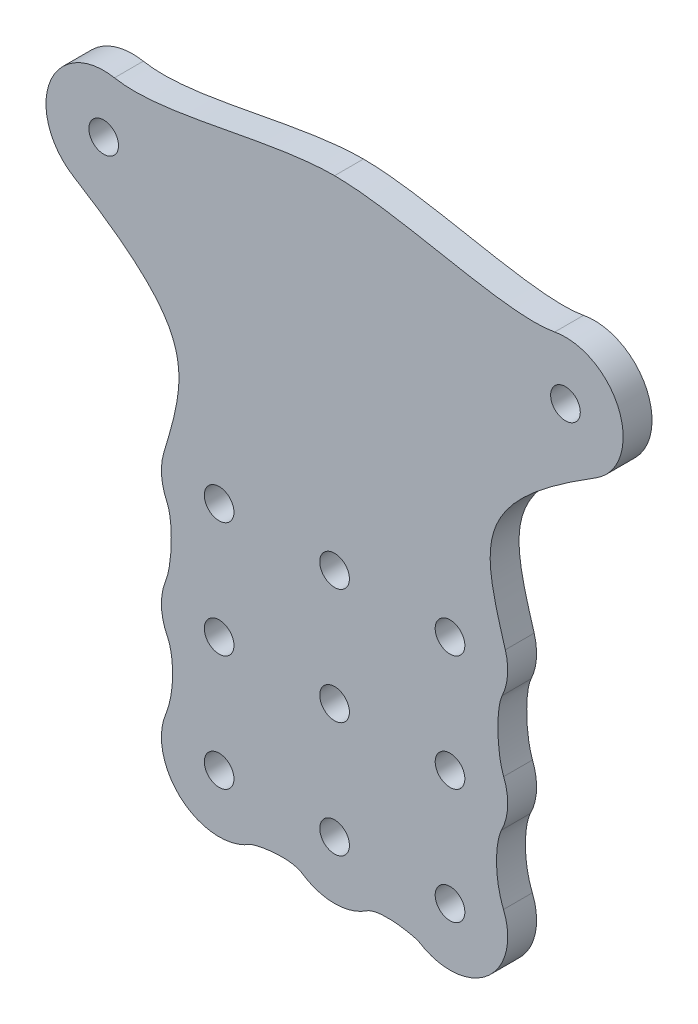
SolidWorks part; units mm, degrees
material "6061-T6 (SS)"
ref_plane "Front Plane" through (0, 0, 0) normal (0, 0, 1) x (1, 0, 0)
ref_plane "Top Plane" through (0, 0, 0) normal (0, 1, 0) x (1, 0, 0)
ref_plane "Right Plane" through (0, 0, 0) normal (1, 0, 0) x (0, 0, -1)
sketch "Sketch1" plane through (0, 0, 0) normal (0, 0, 1) x (1, 0, 0)
  line L0 (50.8, 0) -> (-50.8, 0) construction
  line L1 (0, 0) -> (0, -120.65) construction
  line L2 (63.5, 38.1) -> (-63.5, 38.1) construction
  line L3 (63.5, 38.1) -> (63.5, -38.1) construction
  line L4 (63.5, -38.1) -> (-63.5, -38.1) construction
  line L5 (-63.5, 38.1) -> (-63.5, -38.1) construction
  line L6 (63.5, 38.1) -> (-63.5, -38.1) construction
  line L7 (63.5, -38.1) -> (-63.5, 38.1) construction
  line L8 (-25.4, -57.15) -> (0, -57.15) construction
  line L9 (17.958, 18.0474) -> (-17.958, 18.0474) construction
  line L10 (-38.1, -120.65) -> (38.1, -120.65) construction
  line L11 (-38.1, -120.65) -> (-38.1, -38.1) construction
  line L12 (-38.1, -38.1) -> (38.1, -38.1) construction
  line L13 (38.1, -120.65) -> (38.1, -38.1) construction
  line L14 (-38.1, -120.65) -> (38.1, -38.1) construction
  line L15 (-38.1, -38.1) -> (38.1, -120.65) construction
  line L16 (-39.5718, 10.7947) -> (-57.2894, 14.1593) construction
  line L17 (-42.1887, -68.962) -> (-32.7709, -37.4736) construction
  line L18 (-48.3449, -16.4436) -> (-71.4207, -2.1908) construction
  line L19 (-35.193, -66.1555) -> (-38.5769, -58.9863) construction
  line L20 (-25.4, -57.15) -> (-25.4, -82.55) construction
  line L21 (-38.4283, -80.9433) -> (-35.9741, -74.7714) construction
  line L22 (-35.1425, -91.4238) -> (-38.5996, -84.5944) construction
  line L23 (-39.0166, -107.7442) -> (-35.3297, -98.6304) construction
  line L24 (-16.1907, -117.1192) -> (-21.3581, -120.4597) construction
  line L25 (-4.5266, -120.1946) -> (-9.5559, -116.8441) construction
  circle A0 centre (-50.8, 0) radius 3.2639
  circle A1 centre (50.8, 0) radius 3.2639
  circle A2 centre (-25.4, -57.15) radius 3.2639
  circle A3 centre (0, -57.15) radius 3.2639
  circle A4 centre (25.4, -57.15) radius 3.2639
  circle A5 centre (0, -82.55) radius 3.2639
  circle A6 centre (25.4, -82.55) radius 3.2639
  circle A7 centre (0, -107.95) radius 3.2639
  circle A8 centre (25.4, -107.95) radius 3.2639
  circle A9 centre (-25.4, -82.55) radius 3.2639
  circle A10 centre (-25.4, -107.95) radius 3.2639
  circle A11 centre (-50.8, 0) radius 12.7
  circle A12 centre (50.8, 0) radius 12.7
  circle A13 centre (-25.4, -57.15) radius 12.7
  circle A14 centre (0, -57.15) radius 12.7 construction
  circle A15 centre (25.4, -57.15) radius 12.7
  circle A16 centre (0, -82.55) radius 12.7 construction
  circle A17 centre (25.4, -82.55) radius 12.7
  circle A18 centre (0, -107.95) radius 12.7
  circle A19 centre (25.4, -107.95) radius 12.7
  circle A20 centre (-25.4, -82.55) radius 12.7
  circle A21 centre (-25.4, -107.95) radius 12.7
  spline S0 degree 3 poles (-48.4306, 12.477) (-37.3572, 10.3742) (-14.965, 18.0474) (0, 18.0474) knots 0 0 0 0 1 1 1 1
  spline S1 degree 3 poles (-57.4738, -10.8051) (-30.3242, -27.5741) (-32.0433, -35.0408) (-37.5675, -53.5109) knots 0 0 0 0 1 1 1 1
  spline S2 degree 3 poles (-36.8849, -62.5709) (-35.475, -65.5581) (-35.6673, -73.9999) (-37.2012, -77.8574) knots 0 0 0 0 1 1 1 1
  spline S3 degree 3 poles (-36.731, -88.2858) (-35.5295, -90.6592) (-34.8689, -97.4912) (-37.1731, -103.1873) knots 0 0 0 0 1 1 1 1
  spline S4 degree 3 poles (-18.5053, -118.6155) (-17.9417, -118.2512) (-10.1846, -116.4253) (-7.0413, -118.5193) knots 0 0 0 0 1 1 1 1
  spline S5 degree 3 poles (18.5053, -118.6155) (17.9417, -118.2512) (10.1846, -116.4253) (7.0413, -118.5193) knots 0 0 0 0 1 1 1 1
  spline S6 degree 3 poles (36.731, -88.2858) (35.5295, -90.6592) (34.8689, -97.4912) (37.1731, -103.1873) knots 0 0 0 0 1 1 1 1
  spline S7 degree 3 poles (36.8849, -62.5709) (35.475, -65.5581) (35.6673, -73.9999) (37.2012, -77.8574) knots 0 0 0 0 1 1 1 1
  spline S8 degree 3 poles (57.4738, -10.8051) (30.3242, -27.5741) (32.0433, -35.0408) (37.5675, -53.5109) knots 0 0 0 0 1 1 1 1
  spline S9 degree 3 poles (48.4306, 12.477) (37.3572, 10.3742) (14.965, 18.0474) (0, 18.0474) knots 0 0 0 0 1 1 1 1
  point P4 (0, 0)
  point P7 (0, 0)
  point P16 (0, -79.375)
  dimension "D4" = 6.5278
  dimension "D1" = 101.6
  dimension "D2" = 38.1
  dimension "D3" = 25.4
  dimension "D7" = 25.4
  dimension "D8" = 76.2
  dimension "D9" = 12.7
  dimension "D10" = 127
  dimension "D11" = 25.4
  dimension "D12" = 90
  dimension "D13" = 57.15
  dimension "D5" = 3
  dimension "D6" = 3
extrude "Boss-Extrude1" add sketch "Sketch1" along normal blind 6.35 contours A12 S9 S0 A11 S1 A13 A20 A21 A18 A19 A17 A15 S8 A3 A5 | A11 A0 | A12 A1 | A13 A2 | A20 A9 | A21 A10 | A18 A7 | A19 A8 | A17 A6 | A15 A4 | S7 A15 A17 | S6 A17 A19 | S5 A19 A18 | A21 S4 A18 | A20 S3 A21 | A13 S2 A20
